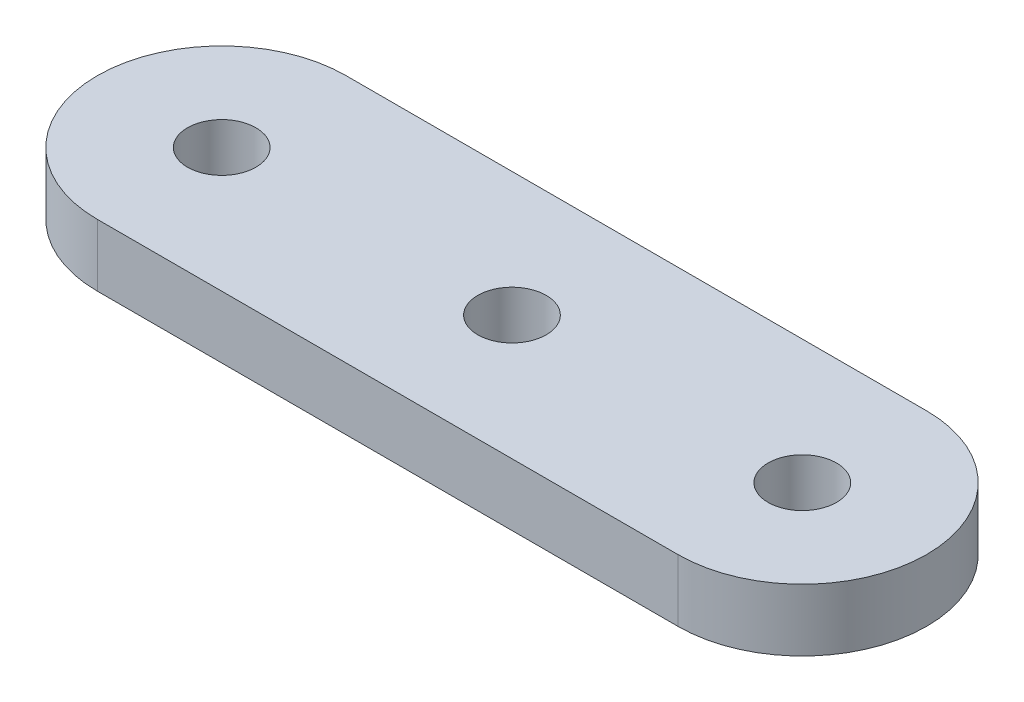
SolidWorks part; units mm, degrees
material "3003 Alloy"
ref_plane "Front Plane" through (0, 0, 0) normal (0, 0, 1) x (1, 0, 0)
ref_plane "Top Plane" through (0, 0, 0) normal (0, 1, 0) x (1, 0, 0)
ref_plane "Right Plane" through (0, 0, 0) normal (1, 0, 0) x (0, 0, -1)
sketch "Sketch1" plane through (0, 0, 0) normal (0, 1, 0) x (1, 0, 0)
  line L0 (-28, 0) -> (0, 0) construction
  line L3 (-28, 6) -> (0, 6)
  line L4 (-28, -6) -> (0, -6)
  line L5 (-14, 6) -> (-14, -6) construction
  arc A2 (-28, 6) -> (-28, -6) centre (-28, 0) ccw
  arc A3 (0, -6) -> (0, 6) centre (0, 0) ccw
  circle A4 centre (-28, 0) radius 2 construction
  circle A5 centre (-14, 0) radius 2 construction
  circle A6 centre (0, 0) radius 2 construction
  point P2 (-14, 0)
  dimension "D1" = 6
  dimension "D2" = 28
  dimension "D3" = 4
  dimension "D4" = 4
extrude "Boss-Extrude2" add sketch "Sketch1" along normal blind 3
sketch "Sketch6" plane through (0, 3, 0) normal (0, 1, 0) x (1, 0, 0)
  point P0 (0, 0)
  point P2 (-14, 0)
  point P4 (-28, 0)
hole_wizard "M4x0.7 Tapped Hole2" positions "Sketch6" profile "Sketch7" tap size "M4x0.7" standard "ANSI Metric"
sketch "Sketch7" plane through (0, 3, 0) normal (1, 0, 0) x (0, 0, 1)
  line L0 (0, 0) -> (0, 11.0914)
  line L1 (0, 11.0914) -> (1.65, 10.1)
  line L2 (1.65, 10.1) -> (1.65, 0)
  line L5 (1.65, 0) -> (0, 0)
  line L10 (0, 11.0914) -> (-1.65, 10.1) construction
  line L11 (0, -6.35) -> (0, 107.95) construction
  dimension "Tap Drill Dia." = 3.3
  dimension "Tap Drill Depth" = 10.1
  dimension "Drill Angle" = 118
cosmetic thread "Hole Thread1" parameters "D1"=8, "D2"=4
cosmetic thread "Hole Thread2" parameters "D1"=8, "D2"=4
cosmetic thread "Hole Thread3" parameters "D1"=8, "D2"=4
